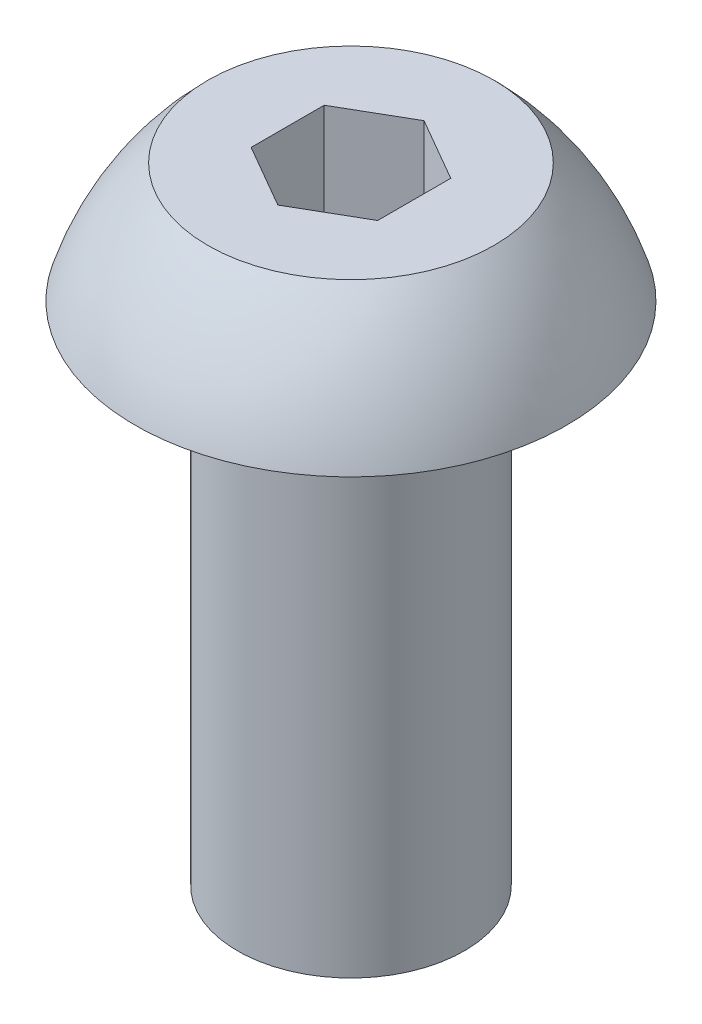
SolidWorks part; units mm, degrees
material "AISI Type 316L stainless steel"
ref_plane "Front Plane" through (0, 0, 0) normal (0, 0, 1) x (1, 0, 0)
ref_plane "Top Plane" through (0, 0, 0) normal (0, 1, 0) x (1, 0, 0)
ref_plane "Right Plane" through (0, 0, 0) normal (1, 0, 0) x (0, 0, -1)
sketch "Sketch1" plane through (0, 0, 0) normal (0, 0, 1) x (1, 0, 0)
  line L0 (-1.4224, 0) -> (-2.7051, 0)
  line L1 (-1.4224, 0) -> (-1.4224, -6.35)
  line L2 (0, -6.35) -> (0, 1.4986)
  line L3 (0, 1.4986) -> (-1.7948, 1.4986)
  line L4 (-1.4224, -6.35) -> (0, -6.35)
  arc A0 (-2.7051, 0) -> (-1.7948, 1.4986) centre (0.7001, -1.0427) cw
  dimension "D1" = 6.35
  dimension "D2" = 1.4986
  dimension "D3" = 2.7051
  dimension "D4" = 1.4224
  dimension "D5" = 1.7948
revolve "Revolve1" add sketch "Sketch1" angle 360 about L2
sketch "Sketch2" plane through (0, 1.4986, 0) normal (0, 1, 0) x (1, 0, 0)
  line L0 (0, 0) -> (0, 0.9165) construction
  line L1 (-0.7938, 0.4583) -> (-0.7937, -0.4583)
  line L2 (-0.7937, -0.4583) -> (0, -0.9165)
  line L3 (0, -0.9165) -> (0.7937, -0.4583)
  line L4 (0.7937, -0.4583) -> (0.7937, 0.4583)
  line L5 (0.7937, 0.4583) -> (0, 0.9165)
  line L6 (0, 0.9165) -> (-0.7938, 0.4583)
  circle A0 centre (0, 0) radius 0.7937 construction
  dimension "D1" = 1.5875
extrude "Cut-Extrude1" cut sketch "Sketch2" against normal blind 1.27
